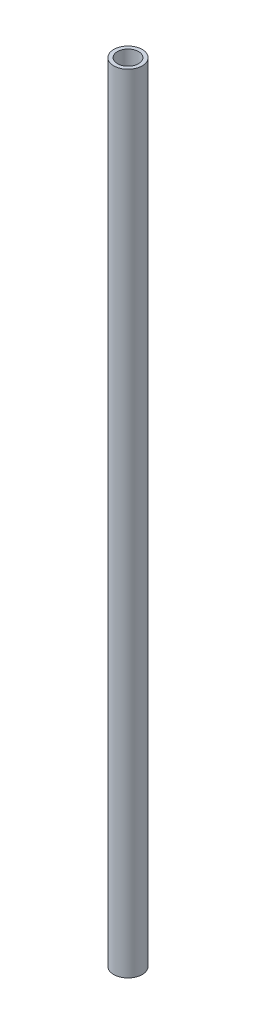
SolidWorks part; units mm, degrees
ref_plane "Front Plane" through (0, 0, 0) normal (0, 0, 1) x (1, 0, 0)
ref_plane "Top Plane" through (0, 0, 0) normal (0, 1, 0) x (1, 0, 0)
ref_plane "Right Plane" through (0, 0, 0) normal (1, 0, 0) x (0, 0, -1)
sketch "Sketch1" plane through (0, 0, 0) normal (0, 1, 0) x (1, 0, 0)
  circle A0 centre (0, 0) radius 7.8994
  circle A1 centre (0, 0) radius 10.668
  dimension "D1" = 15.7988
  dimension "D2" = 21.336
extrude "Boss-Extrude1" add sketch "Sketch1" along normal blind 590
